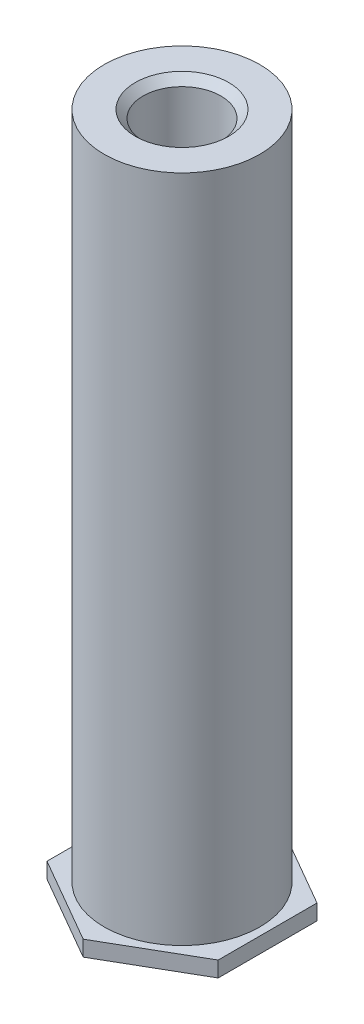
SolidWorks part; units mm, degrees
ref_plane "前视基准面" through (0, 0, 0) normal (0, 0, 1) x (1, 0, 0)
ref_plane "上视基准面" through (0, 0, 0) normal (0, 1, 0) x (1, 0, 0)
ref_plane "右视基准面" through (0, 0, 0) normal (1, 0, 0) x (0, 0, -1)
sketch "草图1" plane through (0, 0, 0) normal (0, 1, 0) x (1, 0, 0)
  line L0 (0, 0) -> (0, 4.5306) construction
  line L1 (0, -3.1754) -> (2.75, -1.5877)
  line L2 (2.75, -1.5877) -> (2.75, 1.5877)
  line L3 (2.75, 1.5877) -> (0, 3.1754)
  line L4 (0, 3.1754) -> (-2.75, 1.5877)
  line L5 (-2.75, 1.5877) -> (-2.75, -1.5877)
  line L6 (-2.75, -1.5877) -> (0, -3.1754)
  circle A0 centre (0, 0) radius 2.75 construction
  dimension "D1" = 5.5
extrude "凸台-拉伸1" add sketch "草图1" along normal blind 0.5
sketch "草图2" plane through (0, 0.5, 0) normal (0, 1, 0) x (1, 0, 0)
  circle A0 centre (0, 0) radius 2.5
  dimension "D1" = 5
extrude "凸台-拉伸2" add sketch "草图2" along normal blind 21.5
hole_wizard "M3 螺纹孔1" positions "草图3" profile "草图4" tap size "M3" standard "GB"
sketch "草图3" plane through (0, 22, 0) normal (0, 1, 0) x (1, 0, 0)
  point P0 (0, 0)
sketch "草图4" plane through (0, 22, 0) normal (1, 0, 0) x (0, 0, 1)
  line L0 (0, 0) -> (0, 8.2511)
  line L1 (0, 8.2511) -> (1.25, 7.5)
  line L2 (1.25, 7.5) -> (1.25, 0.25)
  line L3 (1.25, 0.25) -> (1.5, 0)
  line L5 (1.5, 0) -> (0, 0)
  line L6 (-1.25, 0.25) -> (-1.5, 0) construction
  line L10 (0, 8.2511) -> (-1.25, 7.5) construction
  line L11 (0, -6.35) -> (0, 107.95) construction
  dimension "螺纹孔钻头直径" = 2.5
  dimension "螺纹孔钻头深度" = 7.5
  dimension "近端锥形沉头孔直径" = 3
  dimension "近端锥形沉头孔角度" = 90
  dimension "导头角度" = 118
cosmetic thread "孔螺蚊线1" parameters "D1"=6, "D2"=3
